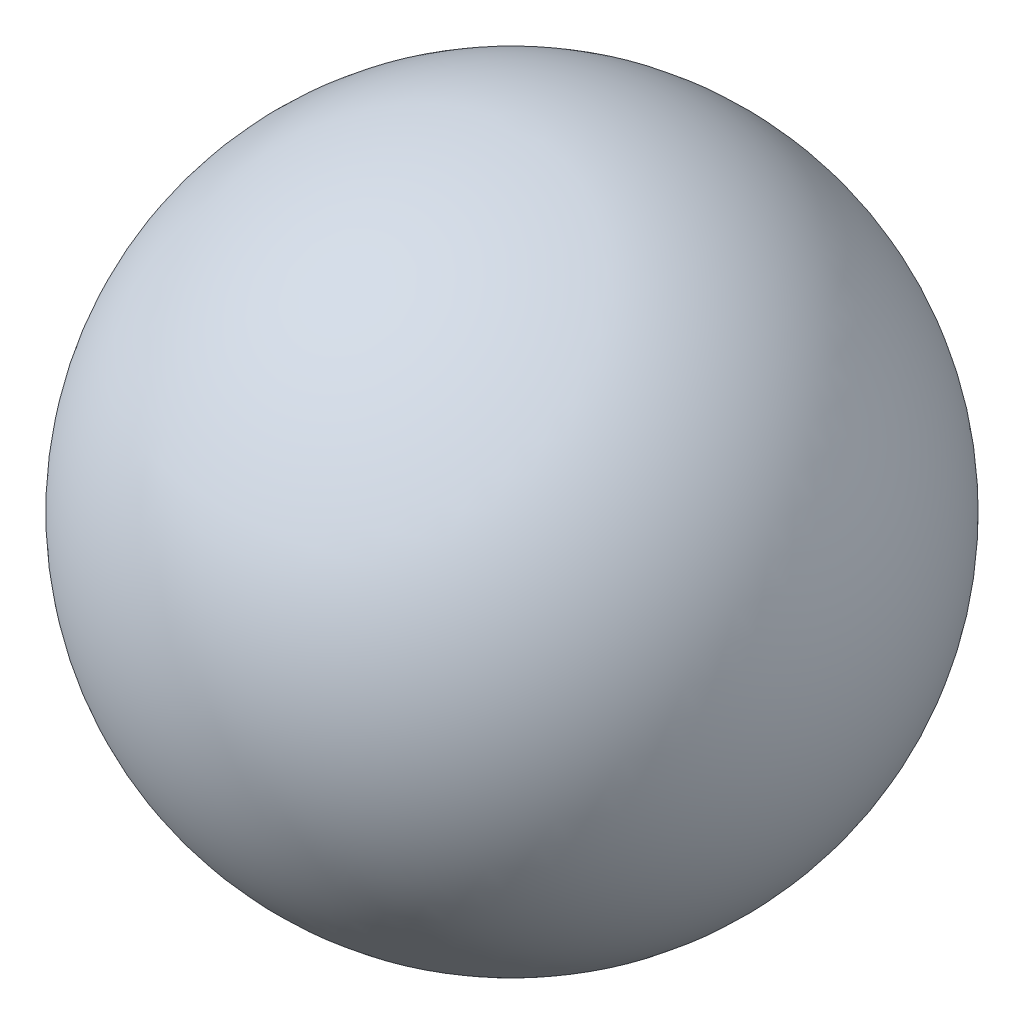
SolidWorks part; units mm, degrees
ref_plane "Front Plane" through (0, 0, 0) normal (0, 0, 1) x (1, 0, 0)
ref_plane "Top Plane" through (0, 0, 0) normal (0, 1, 0) x (1, 0, 0)
ref_plane "Right Plane" through (0, 0, 0) normal (1, 0, 0) x (0, 0, -1)
sketch "Sketch1" plane through (0, 0, 0) normal (0, 0, 1) x (1, 0, 0)
  line L0 (0, -21.5) -> (0, 21.5)
  line L1 (0, -30.1251) -> (0, 30.8782) construction
  line L2 (0, -21.5) -> (0, 21.5)
  arc A0 (0, 21.5) -> (0, -21.5) centre (0, 0) ccw
  dimension "D1" = 43
revolve "Revolve5" add sketch "Sketch1" angle 360 about L1
